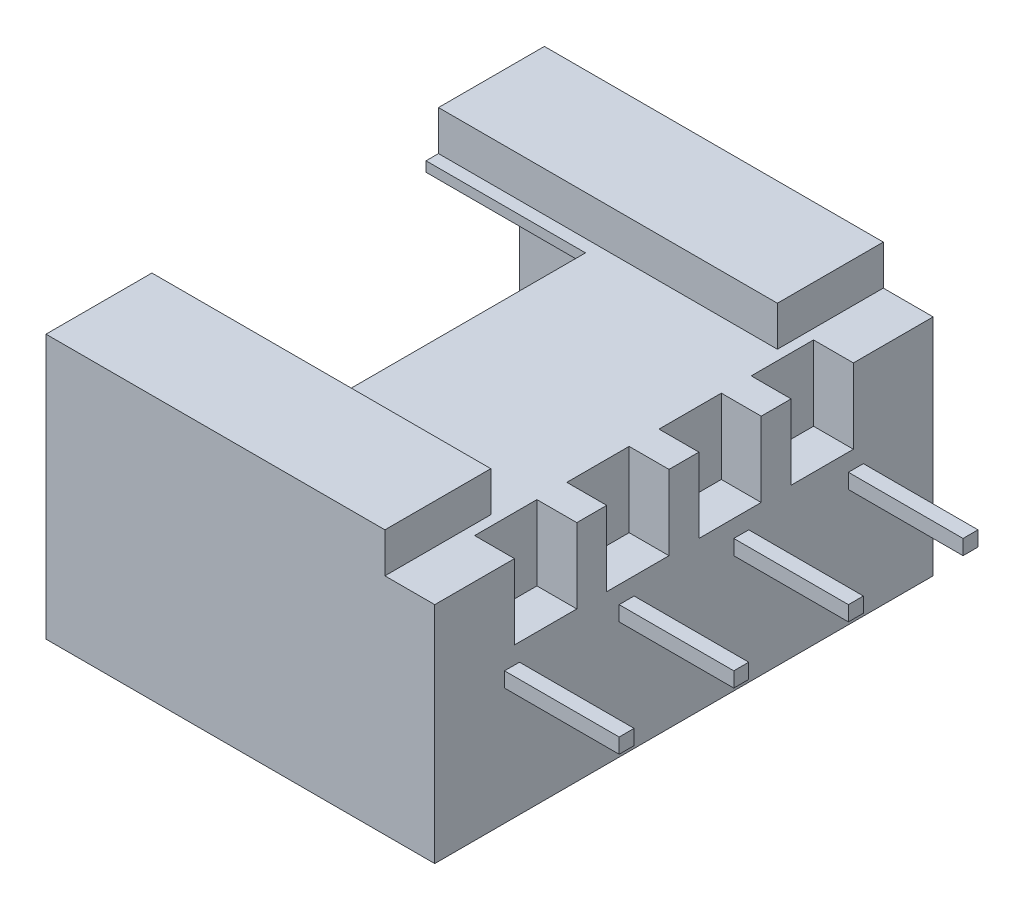
SolidWorks part; units mm, degrees
ref_plane "Plan de face" through (0, 0, 0) normal (0, 0, 1) x (1, 0, 0)
ref_plane "Plan de dessus" through (0, 0, 0) normal (0, 1, 0) x (1, 0, 0)
ref_plane "Plan de droite" through (0, 0, 0) normal (1, 0, 0) x (0, 0, -1)
ref_plane "Plan2" through (0, 0, -3.6) normal (0, 0, -1) x (-1, 0, 0)
sketch "Esquisse7" plane through (0, 0, -3.6) normal (0, 0, -1) x (-1, 0, 0)
  line L0 (-11.55, 3.1) -> (-3.55, 3.1)
  line L1 (-3.55, 3.1) -> (-3.55, 3.4)
  line L2 (-3.55, 3.4) -> (-11.55, 3.4)
  line L3 (-11.55, 3.4) -> (-11.55, 3.1)
  dimension "D1" = 8
  dimension "D2" = 0.3
  dimension "D3" = 3.1
  dimension "D4" = 3.55
extrude "Boss.-Extru.2" add sketch "Esquisse7" against normal blind 0.3 separate body
ref_plane "Plan3" through (0, 6.05, 0) normal (0, 1, 0) x (1, 0, 0)
sketch "Esquisse12" plane through (0, 6.05, 0) normal (0, 1, 0) x (1, 0, 0)
  line L0 (1.45, 5) -> (1.45, -5)
  line L1 (1.45, -5) -> (9.25, -5)
  line L2 (9.25, -5) -> (9.25, 5)
  line L3 (9.25, 5) -> (1.45, 5)
  line L4 (-0.8887, 0) -> (10.5397, 0) construction
  dimension "D1" = 10
extrude "Boss.-Extru.3" add sketch "Esquisse12" against normal blind 5.3 separate body
sketch "Esquisse13" plane through (1.45, 0, 0) normal (-1, 0, 0) x (0, 0, 1)
  line L0 (-4.5, 5.55) -> (-4.5, 1.25)
  line L1 (-4.5, 1.25) -> (4.5, 1.25)
  line L2 (4.5, 1.25) -> (4.5, 5.55)
  line L3 (4.5, 5.55) -> (3.5, 5.55)
  line L4 (3.5, 5.55) -> (3.5, 5.05)
  line L5 (3.5, 5.05) -> (-3.5, 5.05)
  line L6 (-3.5, 5.05) -> (-3.5, 5.55)
  line L7 (-3.5, 5.55) -> (-4.5, 5.55)
  line L8 (0, -0.6971) -> (0, 6.7234) construction
  line L9 (-5, 0.75) -> (5, 0.75) construction
  line L10 (-5, 6.05) -> (5, 6.05) construction
  point P11 (-3.5, 5.3)
  point P12 (3.5, 5.3)
  dimension "D1" = 9
  dimension "D2" = 7
  dimension "D3" = 0.5
  dimension "D4" = 0.5
  dimension "D5" = 0.5
extrude "Enlèv. mat.-Extru.3" cut sketch "Esquisse13" against normal blind 6.1
sketch "Esquisse14" plane through (0, 6.05, 0) normal (0, 1, 0) x (-1, 0, 0)
  line L0 (-1.45, 2.625) -> (-4.65, 2.625)
  line L1 (-4.65, 2.625) -> (-4.65, -2.625)
  line L2 (-4.65, -2.625) -> (-1.45, -2.625)
  line L3 (-1.45, -2.625) -> (-1.45, 2.625)
  line L4 (1.0836, 0) -> (-10.1804, 0) construction
  line L5 (-1.45, -5) -> (-1.45, 5) construction
  dimension "D1" = 3.2
  dimension "D2" = 5.25
extrude "Enlèv. mat.-Extru.4" cut sketch "Esquisse14" against normal up to next (1 mm away)
pattern_linear "Répétition linéaire1" count 4 spacing 2.3 along (0, 0, 1) of "Boss.-Extru.2"
sketch "Esquisse15" plane through (0, 6.05, 0) normal (0, 1, 0) x (1, 0, 0)
  line L0 (-1.4029, 0) -> (6.993, 0) construction
  line L1 (4.65, -2.625) -> (4.65, 2.625) construction
  line L2 (1.2527, 2.875) -> (4.65, 2.875)
  line L3 (1.2527, 2.875) -> (1.2527, -2.875)
  line L4 (1.2527, -2.875) -> (4.65, -2.875)
  line L5 (4.65, 2.875) -> (4.65, -2.875)
  line L6 (4.65, 2.625) -> (1.45, 2.625) construction
  dimension "D1" = 0.25
extrude "Enlèv. mat.-Extru.5" cut sketch "Esquisse15" against normal blind 0.8
sketch "Esquisse16" plane through (0, 6.05, 0) normal (0, 1, 0) x (1, 0, 0)
  line L0 (-1.2358, 0) -> (9.9169, 0) construction
  line L1 (1.45, -2.875) -> (4.65, -2.875) construction
  line L2 (1.45, 2.875) -> (10.9611, 2.875)
  line L3 (1.45, 2.875) -> (1.45, -2.875)
  line L4 (1.45, -2.875) -> (10.9611, -2.875)
  line L5 (10.9611, 2.875) -> (10.9611, -2.875)
extrude "Enlèv. mat.-Extru.6" cut sketch "Esquisse16" against normal blind 0.8
sketch "Esquisse17" plane through (0, 6.05, 0) normal (0, 1, 0) x (1, 0, 0)
  line L0 (9.25, 2.875) -> (9.25, 5) construction
  line L1 (8.25, 5.3466) -> (10.3273, 5.3466)
  line L2 (8.25, 5.3466) -> (8.25, -5.3327)
  line L3 (8.25, -5.3327) -> (10.3273, -5.3327)
  line L4 (10.3273, 5.3466) -> (10.3273, -5.3327)
  dimension "D1" = 1
extrude "Enlèv. mat.-Extru.7" cut sketch "Esquisse17" against normal up to surface (0.8 mm away) up to face at (4.2, 5.25, 0)
sketch "Esquisse18" plane through (0, 5.25, 0) normal (0, 1, 0) x (1, 0, 0)
  line L0 (-0.868, 0) -> (10.4248, 0) construction
  line L1 (9.25, 5) -> (9.25, -5) construction
  line L2 (8.45, 1.55) -> (9.75, 1.55)
  line L3 (8.45, 1.55) -> (8.45, 0.3)
  line L4 (8.45, 0.3) -> (9.75, 0.3)
  line L5 (9.75, 1.55) -> (9.75, 0.3)
  line L6 (8.45, 3.4) -> (9.75, 3.4)
  line L7 (8.45, 3.4) -> (8.45, 2.15)
  line L8 (8.45, 2.15) -> (9.75, 2.15)
  line L9 (9.75, 3.4) -> (9.75, 2.15)
  line L10 (9.75, -3.4) -> (9.75, -2.15)
  line L11 (8.45, -3.4) -> (9.75, -3.4)
  line L12 (8.45, -3.4) -> (8.45, -2.15)
  line L13 (8.45, -2.15) -> (9.75, -2.15)
  line L14 (9.75, -1.55) -> (9.75, -0.3)
  line L15 (8.45, -1.55) -> (9.75, -1.55)
  line L16 (8.45, -0.3) -> (9.75, -0.3)
  line L17 (8.45, -1.55) -> (8.45, -0.3)
  point P11 (8.45, 2.775)
  point P14 (9.75, 0.925)
  point P15 (9.75, 2.775)
  dimension "D1" = 1.25
  dimension "D2" = 1.25
  dimension "D3" = 0.3
  dimension "D4" = 0.6
  dimension "D5" = 0.8
  dimension "D6" = 1.3
extrude "Enlèv. mat.-Extru.8" cut sketch "Esquisse18" against normal blind 1.5
